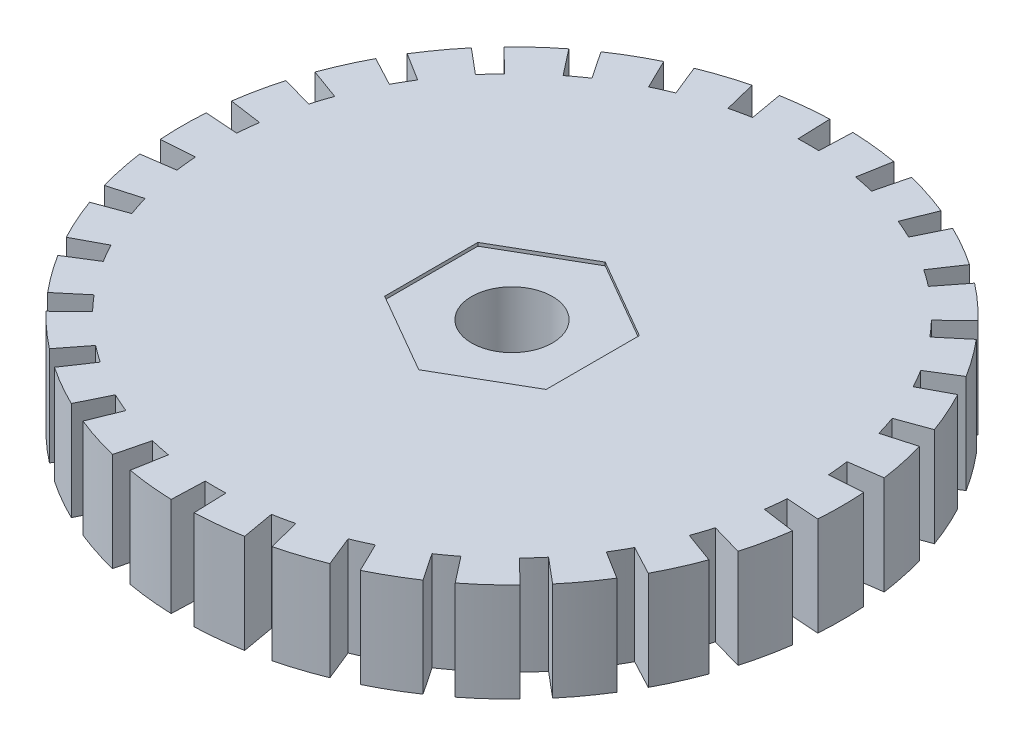
SolidWorks part; units mm, degrees
ref_plane "Front Plane" through (0, 0, 0) normal (0, 0, 1) x (1, 0, 0)
ref_plane "Top Plane" through (0, 0, 0) normal (0, 1, 0) x (1, 0, 0)
ref_plane "Right Plane" through (0, 0, 0) normal (1, 0, 0) x (0, 0, -1)
sketch "Sketch1" plane through (0, 0, 0) normal (0, 1, 0) x (1, 0, 0)
  line L1 (0, -2.829) -> (2.45, -1.4145)
  line L2 (2.45, -1.4145) -> (2.45, 1.4145)
  line L3 (2.45, 1.4145) -> (0, 2.829)
  line L4 (0, 2.829) -> (-2.45, 1.4145)
  line L5 (-2.45, 1.4145) -> (-2.45, -1.4145)
  line L6 (-2.45, -1.4145) -> (0, -2.829)
  circle A0 centre (0, 0) radius 2.45 construction
  circle A1 centre (0, 0) radius 1.225
  dimension "D1" = 2.45
  dimension "D2" = 4.9
extrude "Boss-Extrude1" add sketch "Sketch1" along normal blind 1.9
sketch "Sketch2" plane through (0, 0, 0) normal (0, 1, 0) x (1, 0, 0)
  line L6 (-2.45, -1.4145) -> (0, -2.829)
  line L7 (0, -2.829) -> (2.45, -1.4145)
  line L8 (2.45, -1.4145) -> (2.45, 1.4145)
  line L9 (2.45, 1.4145) -> (0, 2.829)
  line L10 (0, 2.829) -> (-2.45, 1.4145)
  line L11 (-2.45, 1.4145) -> (-2.45, -1.4145)
  line L12 (-2.45, -1.4145) -> (0, -2.829)
  line L13 (0, -2.829) -> (2.45, -1.4145)
  line L14 (2.45, -1.4145) -> (2.45, 1.4145)
  line L15 (2.45, 1.4145) -> (0, 2.829)
  line L16 (0, 2.829) -> (-2.45, 1.4145)
  line L17 (-2.45, 1.4145) -> (-2.45, -1.4145)
  circle A0 centre (0, 0) radius 10
  dimension "D2" = 20
  dimension "D1" = 0
extrude "Boss-Extrude2" add sketch "Sketch2" along normal blind 2 separate body
sketch "Sketch3" plane through (0, 0, 0) normal (0, -1, 0) x (1, 0, 0)
  circle A0 centre (0, 0) radius 10 construction
  circle A1 centre (0, 0) radius 10
  circle A2 centre (0, 0) radius 1.3
  dimension "D1" = 2.6
extrude "Boss-Extrude3" add sketch "Sketch3" along normal blind 1
sketch "Sketch4" plane through (0, 2, 0) normal (0, 1, 0) x (1, 0, 0)
  line L0 (0, 0) -> (0, -11.1233) construction
  line L1 (0, 0) -> (-0.349, -9.9939)
  line L2 (-0.349, -9.9939) -> (-0.349, -10.6518)
  line L3 (-0.349, -10.6518) -> (0.349, -10.6518)
  line L4 (0.349, -10.6518) -> (0.349, -9.9939)
  line L5 (0.349, -9.9939) -> (0, 0)
  circle A0 centre (0, 0) radius 10 construction
  circle A3 centre (0, 0) radius 9
  circle A4 centre (0, 0) radius 9
  circle M5 centre (0, 0) radius 10
  dimension "D1" = 1
  dimension "D2" = 2
  dimension "D3" = 2
extrude "Cut-Extrude1" cut sketch "Sketch4" against normal blind 10 contours L0 L2 L3 M5 | L0 L3 L4 M5 | A4 L0 L5 M5 | L0 A4 L1 M5
pattern_circular "CirPattern1" count 30 over 360 about axis through (0, 0, 0) along (0, 1, 0) of "Cut-Extrude1"
